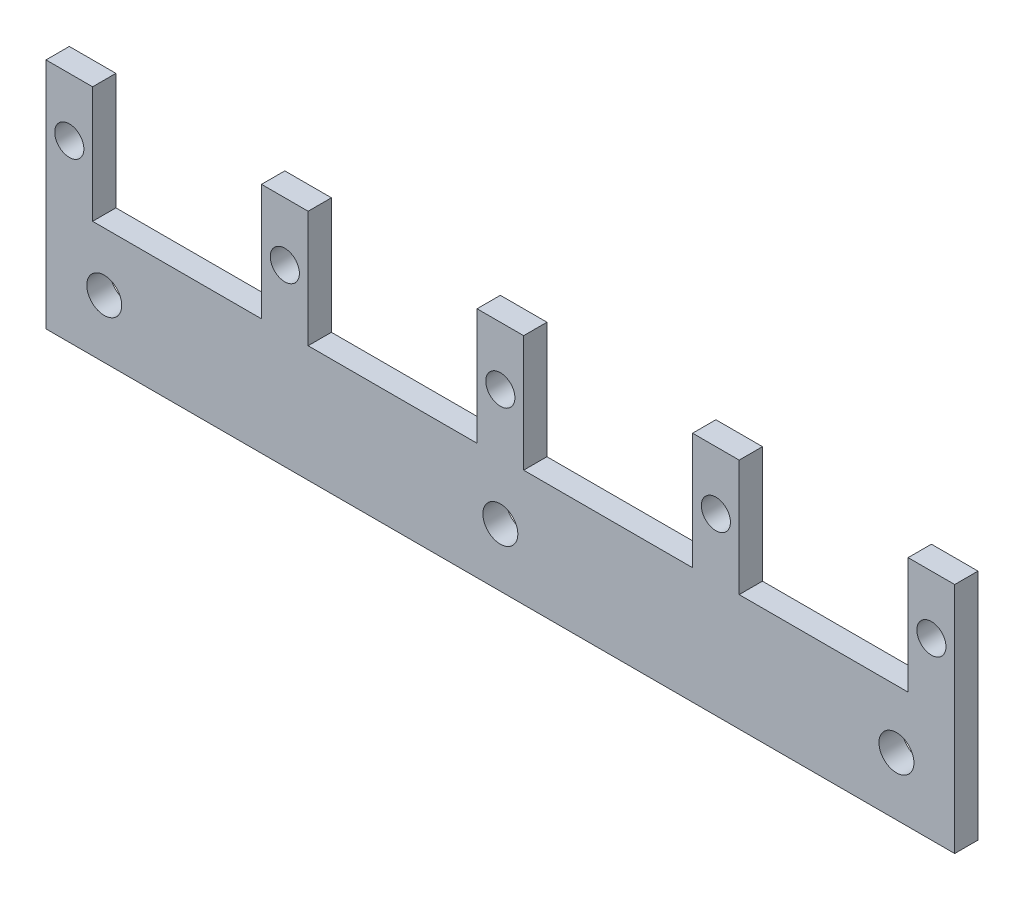
SolidWorks part; units mm, degrees
ref_plane "Front Plane" through (0, 0, 0) normal (0, 0, 1) x (1, 0, 0)
ref_plane "Top Plane" through (0, 0, 0) normal (0, 1, 0) x (1, 0, 0)
ref_plane "Right Plane" through (0, 0, 0) normal (1, 0, 0) x (0, 0, -1)
sketch "Sketch1" plane through (0, 0, 0) normal (0, 0, 1) x (1, 0, 0)
  line L0 (69, 12.4428) -> (69, 32.4428)
  line L1 (-50, -7.5572) -> (106, -7.5572)
  line L2 (-50, -7.5572) -> (-50, 12.4428)
  line L3 (-50, 12.4428) -> (106, 12.4428)
  line L4 (106, -7.5572) -> (106, 12.4428)
  line L5 (-50, -7.5572) -> (106, 12.4428) construction
  line L6 (-50, 12.4428) -> (106, -7.5572) construction
  line L7 (106, 12.4428) -> (98, 12.4428)
  line L8 (106, 12.4428) -> (106, 32.4428)
  line L9 (106, 32.4428) -> (98, 32.4428)
  line L10 (98, 12.4428) -> (98, 32.4428)
  line L11 (69, 12.4428) -> (61, 12.4428)
  line L12 (61, 12.4428) -> (61, 32.4428)
  line L13 (69, 32.4428) -> (61, 32.4428)
  line L14 (32, 12.4428) -> (32, 32.4428)
  line L15 (32, 12.4428) -> (24, 12.4428)
  line L16 (24, 12.4428) -> (24, 32.4428)
  line L17 (32, 32.4428) -> (24, 32.4428)
  line L18 (-5, 12.4428) -> (-5, 32.4428)
  line L19 (-5, 12.4428) -> (-13, 12.4428)
  line L20 (-13, 12.4428) -> (-13, 32.4428)
  line L21 (-5, 32.4428) -> (-13, 32.4428)
  line L22 (-42, 12.4428) -> (-42, 32.4428)
  line L23 (-42, 12.4428) -> (-50, 12.4428)
  line L24 (-50, 12.4428) -> (-50, 32.4428)
  line L25 (-42, 32.4428) -> (-50, 32.4428)
  point P0 (28, 2.4428)
  dimension "D1" = 156
  dimension "D2" = 20
  dimension "D3" = 8
  dimension "D4" = 20
  dimension "D5" = 5
extrude "Boss-Extrude1" add sketch "Sketch1" along normal mid plane 4 contours L1 L4 L3 L2 | L10 L3 L8 L9 | L0 L13 L12 L3 | L14 L17 L16 L3 | L18 L21 L20 L3 | L22 L25 L24 L3
sketch "Sketch2" plane through (0, 0, 2) normal (0, 0, 1) x (1, 0, 0)
  line L0 (-50, 32.4428) -> (-42, 12.4428) construction
  line L1 (-42, 32.4428) -> (-50, 12.4428) construction
  line L2 (-50, -7.5572) -> (-50, 32.4428) construction
  line L3 (-50, 12.4428) -> (-42, 12.4428) construction
  circle A0 centre (-46, 22.4428) radius 2.5
  dimension "D1" = 5
extrude "Cut-Extrude1" cut sketch "Sketch2" against normal through all
fillet "Fillet1" [suppressed] radius 1
fillet "Fillet2" [suppressed] radius 1
pattern_linear "LPattern1" count 5 spacing 37 along (1, 0, 0) of "Cut-Extrude1", "Fillet2"
sketch "Sketch3" plane through (0, 0, 2) normal (0, 0, 1) x (1, 0, 0)
  line L0 (28, -7.5572) -> (28, 12.4428) construction
  line L1 (-50, -7.5572) -> (106, -7.5572) construction
  line L2 (24, 12.4428) -> (32, 12.4428) construction
  line L3 (24, 12.4428) -> (24, 32.4428) construction
  line L4 (-40, 2.4428) -> (96, 2.4428) construction
  line L5 (106, -7.5572) -> (106, 32.4428) construction
  circle A0 centre (28, 2.4428) radius 3
  circle A1 centre (96, 2.4428) radius 3
  circle A2 centre (-40, 2.4428) radius 3
  point P8 (28, 12.4428)
  point P13 (28, 2.4428)
  dimension "D1" = 6
  dimension "D2" = 10
extrude "Cut-Extrude2" cut sketch "Sketch3" against normal through all
